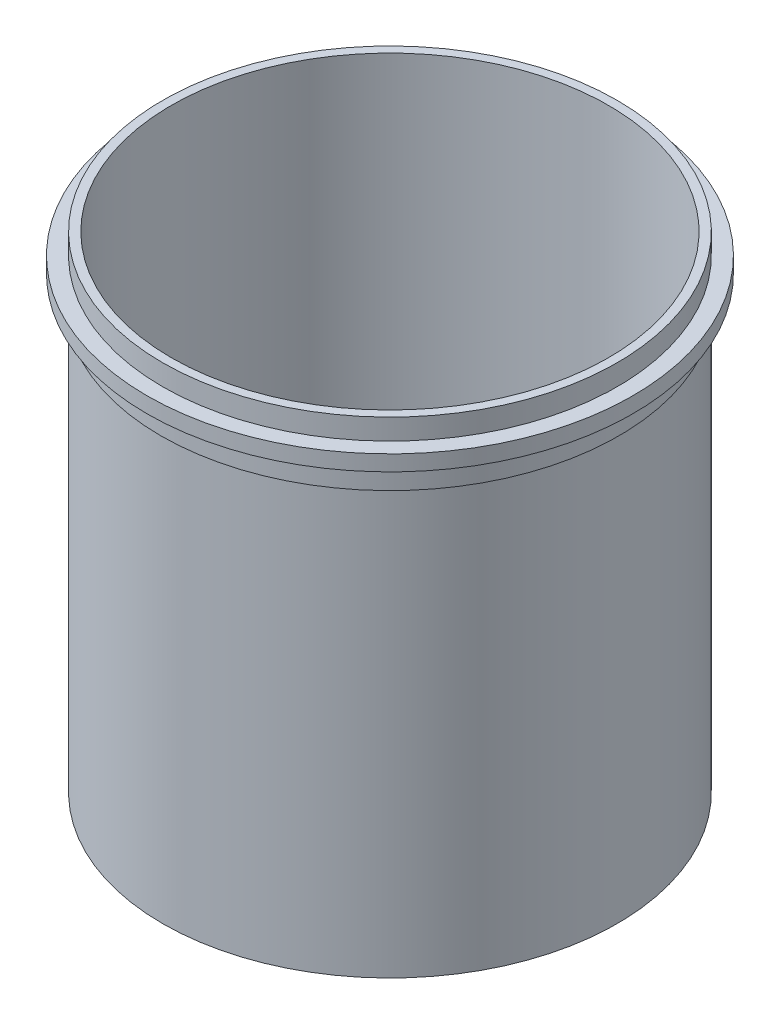
SolidWorks part; units mm, degrees
material "3.3315 (EN-AW 5005)"
ref_plane "Front Plane" through (0, 0, 0) normal (0, 0, 1) x (1, 0, 0)
ref_plane "Top Plane" through (0, 0, 0) normal (0, 1, 0) x (1, 0, 0)
ref_plane "Right Plane" through (0, 0, 0) normal (1, 0, 0) x (0, 0, -1)
sketch "Sketch1" plane through (0, 0, 0) normal (0, 1, 0) x (1, 0, 0)
  circle A0 centre (0, 0) radius 131
  circle A1 centre (0, 0) radius 126
  dimension "D1" = 252
  dimension "D2" = 5
extrude "Boss-Extrude1" add sketch "Sketch1" against normal blind 280
ref_plane "Plane1" through (0, 0, 131) normal (0, 0, 1) x (1, 0, 0)
ref_plane "Plane2" through (0, -12, 0) normal (0, 1, 0) x (1, 0, 0)
sketch "Sketch4" plane through (0, -12, 0) normal (0, 1, 0) x (1, 0, 0)
  circle A0 centre (0, 0) radius 131 construction
  circle A1 centre (0, 0) radius 131
  circle A2 centre (0, 0) radius 140
  dimension "D1" = 9
extrude "Boss-Extrude2" add sketch "Sketch4" against normal blind 9
chamfer "Chamfer1" distance 20 angle 10 1 edges at (0, -280, 126)
sketch "Sketch5" plane through (0, -21, 0) normal (0, -1, 0) x (1, 0, 0)
  circle A0 centre (0, 0) radius 131 construction
  circle A1 centre (0, 0) radius 131
  circle A4 centre (0, 0) radius 132
  circle A5 centre (0, 0) radius 132
  dimension "D1" = 1
extrude "Boss-Extrude3" add sketch "Sketch5" along normal blind 15
